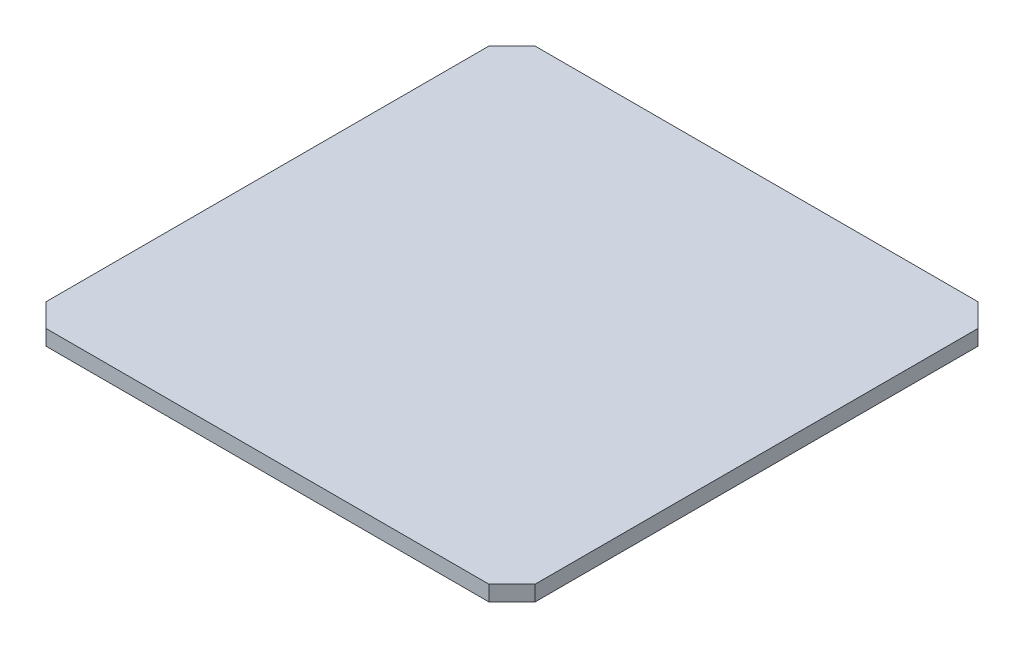
SolidWorks part; units mm, degrees
ref_plane "Plan de face" through (0, 0, 0) normal (0, 0, 1) x (1, 0, 0)
ref_plane "Plan de dessus" through (0, 0, 0) normal (0, 1, 0) x (1, 0, 0)
ref_plane "Plan de droite" through (0, 0, 0) normal (1, 0, 0) x (0, 0, -1)
sketch "Esquisse1" plane through (0, 0, 0) normal (0, 1, 0) x (1, 0, 0)
  line L1 (0, 0) -> (25.4, 0)
  line L2 (0, 0) -> (0, 25.4)
  line L3 (0, 25.4) -> (25.4, 25.4)
  line L4 (25.4, 0) -> (25.4, 25.4)
  dimension "D1" = 25.4
  dimension "D2" = 25.4
extrude "Boss.-Extru.1" add sketch "Esquisse1" along normal blind 0.8
chamfer "Chanfrein1" distance 1.2 angle 45 4 edges at (0, 0.4, -25.4) (0, 0.4, 0) (25.4, 0.4, 0) (25.4, 0.4, -25.4)
